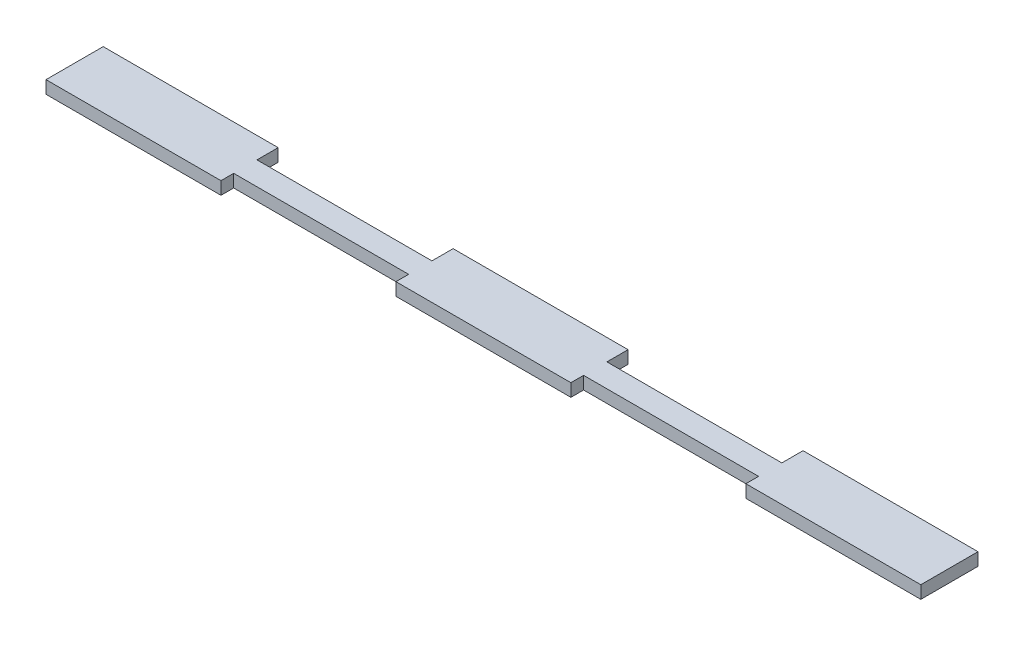
SolidWorks part; units mm, degrees
ref_plane "Front Plane" through (0, 0, 0) normal (0, 0, 1) x (1, 0, 0)
ref_plane "Top Plane" through (0, 0, 0) normal (0, 1, 0) x (1, 0, 0)
ref_plane "Right Plane" through (0, 0, 0) normal (1, 0, 0) x (0, 0, -1)
sketch "Sketch1" plane through (0, 0, 0) normal (0, 1, 0) x (1, 0, 0)
  line L1 (-103.25, 6.75) -> (-61.95, 6.75)
  line L2 (-103.25, 6.75) -> (-103.25, -6.75)
  line L3 (-103.25, -6.75) -> (-61.95, -6.75)
  line L4 (103.25, 6.75) -> (103.25, -6.75)
  line L5 (20.65, -3.75) -> (20.65, -6.75)
  line L6 (-20.65, -3.75) -> (-20.65, -6.75)
  line L7 (-61.95, 1.75) -> (-20.65, 1.75)
  line L9 (-61.95, -3.75) -> (-20.65, -3.75)
  line L11 (-20.65, -6.75) -> (20.65, -6.75)
  line L13 (61.95, -6.75) -> (103.25, -6.75)
  line L15 (-20.65, 6.75) -> (20.65, 6.75)
  line L17 (61.95, 6.75) -> (103.25, 6.75)
  line L18 (-61.95, 6.75) -> (-61.95, 1.75)
  line L19 (-20.65, 6.75) -> (-20.65, 1.75)
  line L20 (20.65, 6.75) -> (20.65, 1.75)
  line L21 (61.95, 6.75) -> (61.95, 1.75)
  line L22 (20.65, 1.75) -> (61.95, 1.75)
  line L23 (61.95, -3.75) -> (61.95, -6.75)
  line L24 (-61.95, -3.75) -> (-61.95, -6.75)
  line L25 (20.65, -3.75) -> (61.95, -3.75)
  point P0 (0, 0)
  dimension "D1" = 206.5
  dimension "D2" = 13.5
extrude "Boss-Extrude1" add sketch "Sketch1" along normal blind 3
